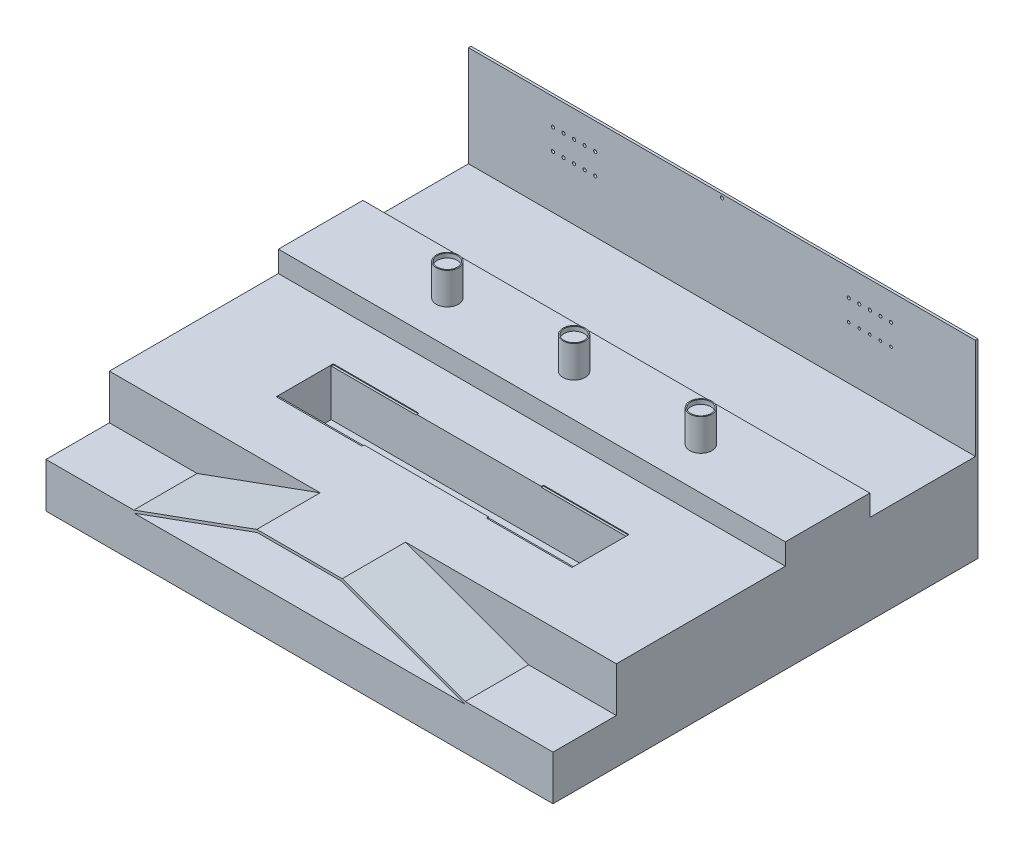
SolidWorks part; units mm, degrees
ref_plane "前视基准面" through (0, 0, 0) normal (0, 0, 1) x (1, 0, 0)
ref_plane "上视基准面" through (0, 0, 0) normal (0, 1, 0) x (1, 0, 0)
ref_plane "右视基准面" through (0, 0, 0) normal (1, 0, 0) x (0, 0, -1)
sketch "草图1" plane through (0, 0, 0) normal (0, 0, 1) x (1, 0, 0)
  line L0 (-200, 0) -> (200, 0)
  line L1 (-200, 0) -> (-782.4652, -212)
  line L2 (200, 0) -> (782.4652, -212)
  line L3 (-1200, -200) -> (-784.5811, -200)
  line L4 (202.1159, 12) -> (784.5811, -200)
  line L5 (-202.1159, 12) -> (202.1159, 12)
  line L6 (-202.1159, 12) -> (-784.5811, -200)
  line L7 (-202.1159, 12) -> (-753.5997, -188.7237) construction
  line L8 (-1200, -212) -> (-782.4652, -212)
  line L9 (-200, 0) -> (-749.4955, -200) construction
  line L10 (202.1159, 12) -> (787.1681, -200.9416) construction
  line L11 (200, 0) -> (783.0639, -212.2179) construction
  line L12 (784.5811, -200) -> (1200, -200)
  line L13 (-1200, -200) -> (1200, -200) construction
  line L14 (782.4652, -212) -> (1200, -212)
  line L15 (-1200, -212) -> (1200, -212) construction
  line L16 (-1200, -200) -> (-1200, -212)
  line L17 (1200, -200) -> (1200, -212)
  point P17 (-1200, -206)
  dimension "D1" = 160
  dimension "D2" = 160
  dimension "D3" = 200
  dimension "D6" = 12
  dimension "D7" = 2400
  dimension "D4" = 12
  dimension "D5" = 12
extrude "凸台-拉伸1" add sketch "草图1" along normal blind 300
sketch "草图2" plane through (0, 0, 0) normal (0, 0, -1) x (-1, 0, 0)
  line L0 (-1200, -212) -> (-1200, 12)
  line L1 (1200, -212) -> (1200, 12)
  line L2 (-1200, -212) -> (1200, -212)
  line L4 (-1200, 12) -> (1200, 12)
  dimension "D1" = 224
extrude "凸台-拉伸2" add sketch "草图2" along normal blind 800
sketch "草图4" plane through (0, 12, 0) normal (0, 1, 0) x (1, 0, 0)
  line L0 (-1200, 800) -> (1200, 800) construction
  line L1 (-700, 300) -> (700, 300)
  line L2 (-700, 300) -> (-700, 550)
  line L3 (-700, 550) -> (700, 550)
  line L4 (700, 300) -> (700, 550)
  line L5 (-1200, 800) -> (-1200, 0) construction
  line L6 (1200, 800) -> (1200, 0) construction
  dimension "D1" = 250
  dimension "D2" = 250
  dimension "D3" = 500
  dimension "D4" = 500
extrude "切除-拉伸1" cut sketch "草图4" against normal through all
sketch "草图7" plane through (0, 0, -800) normal (0, 0, -1) x (-1, 0, 0)
  line L0 (-1200, -212) -> (-1200, 112)
  line L1 (-1200, 112) -> (1200, 112)
  line L2 (1200, 112) -> (1200, -212)
  line L3 (1200, -212) -> (-1200, -212)
  line L4 (1200, 12) -> (-1200, 12) construction
  dimension "D1" = 100
extrude "凸台-拉伸3" add sketch "草图7" along normal blind 400
sketch "草图8" plane through (0, 112, 0) normal (0, 1, 0) x (1, 0, 0)
  line L1 (-1200, 800) -> (1200, 800) construction
  circle A0 centre (0, 1000) radius 75
  dimension "D1" = 200
extrude "凸台-拉伸4" [suppressed] add sketch "草图8" along normal blind 150
sketch "草图9" plane through (0, 0, -1200) normal (0, 0, -1) x (-1, 0, 0)
  line L0 (1200, -212) -> (1200, 112) construction
  line L1 (-1200, -212) -> (1200, -212)
  line L2 (-1200, -212) -> (-1200, 12)
  line L3 (-1200, 12) -> (1200, 12)
  line L4 (1200, -212) -> (1200, 12)
  line L5 (1200, 112) -> (-1200, 112) construction
  dimension "D1" = 100
extrude "凸台-拉伸5" add sketch "草图9" along normal blind 500
sketch "草图10" plane through (0, 0, -1700) normal (0, 0, -1) x (-1, 0, 0)
  line L0 (-1200, 488) -> (1200, 488)
  line L1 (-1200, -212) -> (1200, -212)
  line L5 (-1200, 488) -> (-1200, -212)
  line L6 (1200, 488) -> (1200, -212)
  line L7 (1200, 12) -> (-1200, 12) construction
  dimension "D1" = 700
  dimension "D2" = 224
extrude "凸台-拉伸6" add sketch "草图10" along normal blind 12
sketch "草图11" plane through (0, 0, -1700) normal (0, 0, 1) x (1, 0, 0)
  line L0 (-1200, 12) -> (-1200, 488) construction
  line L1 (-1200, 488) -> (1200, 488) construction
  line L2 (1200, 488) -> (1200, 12) construction
  circle A0 centre (-600, 463) radius 25
  circle A1 centre (600, 463) radius 25
  dimension "D1" = 600
  dimension "D2" = 25
  dimension "D3" = 600
  dimension "D4" = 25
extrude "凸台-拉伸7" [suppressed] add sketch "草图11" along normal blind 20
sketch "草图12" plane through (0, -212, 0) normal (0, -1, 0) x (1, 0, 0)
  line L1 (-1200, 300) -> (1200, 300)
  line L2 (-1200, 300) -> (-1200, -1712)
  line L3 (-1200, -1712) -> (1200, -1712)
  line L4 (1200, 300) -> (1200, -1712)
extrude "凸台-拉伸8" add sketch "草图12" along normal blind 200
sketch "草图13" plane through (0, 112, 0) normal (0, 1, 0) x (1, 0, 0)
  line L0 (-1200, 1200) -> (-1200, 800) construction
  line L1 (1200, 1200) -> (1200, 800) construction
  line L2 (-1200, 1200) -> (1200, 1200) construction
  line L3 (-1200, 1200) -> (1200, 1200) construction
  circle A0 centre (-600, 1000) radius 52.5
  circle A1 centre (600, 1000) radius 52.5
  circle A2 centre (0, 1000) radius 52.5
  dimension "D1" = 600
  dimension "D2" = 600
  dimension "D3" = 600
  dimension "D4" = 200
  dimension "D5" = 200
  dimension "D6" = 200
extrude "凸台-拉伸9" add sketch "草图13" along normal blind 150
sketch "草图14" plane through (0, 0, -1700) normal (0, 0, 1) x (1, 0, 0)
  line L0 (-1200, 12) -> (-1200, 488) construction
  line L1 (1200, 488) -> (1200, 12) construction
  line L3 (-1200, 12) -> (1200, 12) construction
  circle A0 centre (-800, 262) radius 7.5
  circle A1 centre (800, 362) radius 7.5
  circle A2 centre (-750, 262) radius 7.5
  circle A3 centre (-700, 262) radius 7.5
  circle A4 centre (-650, 262) radius 7.5
  circle A5 centre (-600, 262) radius 7.5
  circle A6 centre (750, 362) radius 7.5
  circle A7 centre (700, 362) radius 7.5
  circle A8 centre (650, 362) radius 7.5
  circle A9 centre (600, 362) radius 7.5
  circle A10 centre (0, 472) radius 7.5
  circle A11 centre (-800, 362) radius 7.5
  circle A12 centre (-750, 362) radius 7.5
  circle A13 centre (-700, 362) radius 7.5
  circle A14 centre (-650, 362) radius 7.5
  circle A15 centre (-600, 362) radius 7.5
  circle A16 centre (800, 262) radius 6.5
  circle A17 centre (750, 262) radius 6.5
  circle A18 centre (700, 262) radius 6.5
  circle A19 centre (650, 262) radius 6.5
  circle A20 centre (600, 262) radius 6.5
  dimension "D1" = 400
  dimension "D2" = 400
  dimension "D3" = 250
  dimension "D7" = 460
  dimension "D8" = 100
  dimension "D9" = 5
  dimension "D10" = 100
  dimension "D4" = 350
  dimension "D5" = 5
  dimension "D6" = 5
extrude "切除-拉伸2" cut sketch "草图14" against normal through all
sketch "草图16" plane through (0, 262, 0) normal (0, 1, 0) x (1, 0, 0)
  circle A0 centre (-600, 1000) radius 47.5
  circle A1 centre (0, 1000) radius 47.5
  circle A2 centre (600, 1000) radius 47.5
extrude "切除-拉伸3" cut sketch "草图16" against normal blind 20
sketch "草图17" plane through (0, 12, 0) normal (0, 1, 0) x (1, 0, 0)
  line L0 (-700, 560) -> (-295, 560)
  line L1 (-700, 550) -> (-295, 550)
  line L2 (-700, 560) -> (-700, 550)
  line L3 (-700, 300) -> (-295, 300)
  line L4 (700, 560) -> (700, 550)
  line L6 (-700, 290) -> (-295, 290)
  line L8 (700, 550) -> (700, 300) construction
  line L9 (-700, 550) -> (-700, 300) construction
  line L10 (710, 560) -> (710, 290) construction
  line L11 (-710, 560) -> (710, 560) construction
  line L12 (700, 300) -> (700, 290)
  line L13 (-710, 290) -> (710, 290) construction
  line L14 (-700, 300) -> (-700, 290)
  line L15 (-710, 560) -> (-710, 290) construction
  line L16 (295, 560) -> (295, 550)
  line L17 (700, 300) -> (700, 550) construction
  line L18 (-295, 560) -> (-295, 550)
  line L19 (-700, 550) -> (-700, 300) construction
  line L20 (295, 560) -> (700, 560)
  line L21 (295, 550) -> (700, 550)
  line L22 (-700, 550) -> (700, 550) construction
  line L23 (295, 300) -> (295, 290)
  line L24 (-295, 300) -> (-295, 290)
  line L25 (295, 300) -> (700, 300)
  line L26 (-700, 300) -> (700, 300) construction
  line L27 (295, 290) -> (700, 290)
  dimension "D2" = 405
  dimension "D3" = 405
  dimension "D1" = 10
extrude "切除-拉伸4" cut sketch "草图17" against normal blind 4
sketch "草图18" plane through (0, 0, -800) normal (0, 0, 1) x (1, 0, 0)
  line L0 (300, 100) -> (-300, 100)
  line L4 (-1200, 112) -> (1200, 112) construction
  line L8 (300, 112) -> (-300, 112)
  line L9 (-300, 112) -> (-473.2051, 12)
  line L10 (-300, 100) -> (-452.4205, 12)
  line L11 (0, 100) -> (0, 40.6933) construction
  line L12 (300, 100) -> (452.4205, 12)
  line L13 (300, 112) -> (473.2051, 12)
  line L14 (-473.2051, 12) -> (-452.4205, 12)
  line L16 (452.4205, 12) -> (473.2051, 12)
  dimension "D2" = 150
  dimension "D3" = 150
  dimension "D1" = 12
extrude "凸台-拉伸10" [suppressed] add sketch "草图18" along normal blind 200
